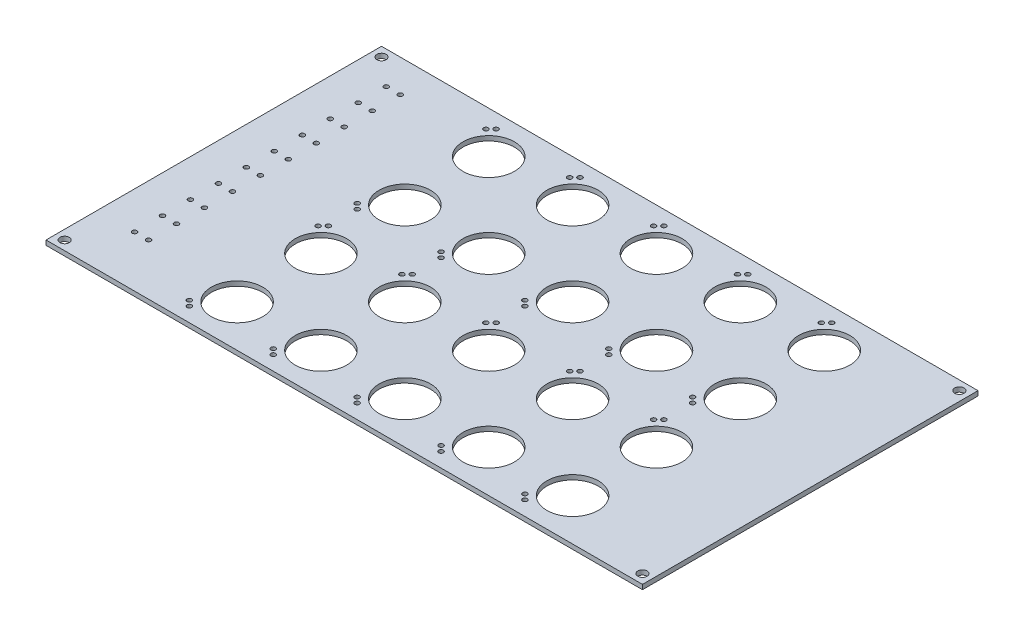
SolidWorks part; units mm, degrees
ref_plane "Front Plane" through (0, 0, 0) normal (0, 0, 1) x (1, 0, 0)
ref_plane "Top Plane" through (0, 0, 0) normal (0, 1, 0) x (1, 0, 0)
ref_plane "Right Plane" through (0, 0, 0) normal (1, 0, 0) x (0, 0, -1)
sketch "Sketch1" plane through (0, 0, 0) normal (0, 1, 0) x (1, 0, 0)
  line L1 (-442.5385, 187.0328) -> (370.2615, 187.0328)
  line L2 (-442.5385, 187.0328) -> (-442.5385, -270.1672)
  line L3 (-442.5385, -270.1672) -> (370.2615, -270.1672)
  line L4 (370.2615, 187.0328) -> (370.2615, -270.1672)
  dimension "D1" = 812.8
  dimension "D2" = 457.2
extrude "Boss-Extrude1" add sketch "Sketch1" along normal blind 6.35
sketch "Sketch3" plane through (0, 6.35, 0) normal (0, 1, 0) x (1, 0, 0)
  line L0 (-442.5385, -270.1672) -> (370.2615, -270.1672) construction
  line L1 (370.2615, -270.1672) -> (370.2615, 187.0328) construction
  line L2 (370.2615, 187.0328) -> (-442.5385, 187.0328) construction
  line L3 (-442.5385, 187.0328) -> (-442.5385, -270.1672) construction
  line L4 (-239.3385, 164.8828) -> (-185.8833, 164.8828) construction
  line L5 (-266.7705, 167.4228) -> (-296.8676, 137.3257) construction
  line L6 (-308.109, 72.7328) -> (304.6709, 72.7328) construction
  line L7 (-266.7705, -21.9572) -> (-296.8676, 8.1399) construction
  line L8 (-442.5385, -41.5672) -> (370.2615, -41.5672) construction
  line L9 (-266.7705, -61.1772) -> (-296.8676, -91.2743) construction
  line L10 (-308.109, -155.8672) -> (304.6709, -155.8672) construction
  line L11 (-266.7705, -250.5572) -> (-296.8676, -220.4601) construction
  line L12 (-239.3385, -248.0172) -> (-185.8833, -248.0172) construction
  circle A0 centre (-239.3385, 129.8828) radius 35
  circle A5 centre (-125.0385, 129.8828) radius 35
  circle A6 centre (-10.7385, 129.8828) radius 35
  circle A7 centre (103.5615, 129.8828) radius 35
  circle A8 centre (217.8615, 129.8828) radius 35
  circle A9 centre (-125.0385, 15.5828) radius 35
  circle A10 centre (-10.7385, 15.5828) radius 35
  circle A11 centre (103.5615, 15.5828) radius 35
  circle A12 centre (217.8615, 15.5828) radius 35
  circle A21 centre (-239.3385, 15.5828) radius 35
  circle A44 centre (-391.7385, 142.5828) radius 3.175
  circle A45 centre (-372.6885, 142.5828) radius 3.175
  circle A46 centre (-372.6885, 104.4828) radius 3.175
  circle A47 centre (-372.6885, 66.3828) radius 3.175
  circle A48 centre (-372.6885, 28.2828) radius 3.175
  circle A49 centre (-372.6885, -9.8172) radius 3.175
  circle A50 centre (-372.6885, -47.9172) radius 3.175
  circle A51 centre (-372.6885, -86.0172) radius 3.175
  circle A52 centre (-372.6885, -124.1172) radius 3.175
  circle A53 centre (-372.6885, -162.2172) radius 3.175
  circle A54 centre (-372.6885, -200.3172) radius 3.175
  circle A55 centre (-391.7385, 104.4828) radius 3.175
  circle A56 centre (-391.7385, 66.3828) radius 3.175
  circle A57 centre (-391.7385, 28.2828) radius 3.175
  circle A58 centre (-391.7385, -9.8172) radius 3.175
  circle A59 centre (-391.7385, -47.9172) radius 3.175
  circle A60 centre (-391.7385, -86.0172) radius 3.175
  circle A61 centre (-391.7385, -124.1172) radius 3.175
  circle A62 centre (-391.7385, -162.2172) radius 3.175
  circle A63 centre (-391.7385, -200.3172) radius 3.175
  circle A64 centre (-429.8385, 174.3328) radius 6.35
  circle A65 centre (-429.8385, -257.4672) radius 6.35
  circle A66 centre (357.5615, -257.4672) radius 6.35
  circle A67 centre (357.5615, 174.3328) radius 6.35
  circle A68 centre (-125.0385, -98.7172) radius 35 [skipped]
  circle A69 centre (-10.7385, -98.7172) radius 35 [skipped]
  circle A70 centre (103.5615, -98.7172) radius 35 [skipped]
  circle A71 centre (217.8615, -98.7172) radius 35 [skipped]
  circle A72 centre (-125.0385, -213.0172) radius 35 [skipped]
  circle A73 centre (-10.7385, -213.0172) radius 35 [skipped]
  circle A74 centre (103.5615, -213.0172) radius 35 [skipped]
  circle A75 centre (-239.3385, -98.7172) radius 35 [skipped]
  circle A76 centre (-239.3385, -213.0172) radius 35 [skipped]
  circle A77 centre (-266.7705, 167.4228) radius 3.175
  circle A79 centre (-273.7751, 160.4182) radius 3.175
  circle A80 centre (-152.4705, 167.4228) radius 3.175
  circle A81 centre (-159.4751, 160.4182) radius 3.175
  circle A82 centre (-38.1705, 167.4228) radius 3.175
  circle A83 centre (-45.1751, 160.4182) radius 3.175
  circle A84 centre (76.1295, 167.4228) radius 3.175
  circle A85 centre (69.1249, 160.4182) radius 3.175
  circle A86 centre (190.4295, 167.4228) radius 3.175
  circle A87 centre (217.8615, -213.0172) radius 35 [skipped]
  circle A88 centre (183.4249, 160.4182) radius 3.175
  circle A89 centre (190.4295, -21.9572) radius 3.175
  circle A90 centre (76.1295, -21.9572) radius 3.175
  circle A91 centre (69.1249, -14.9526) radius 3.175
  circle A92 centre (183.4249, -14.9526) radius 3.175
  circle A93 centre (-38.1705, -21.9572) radius 3.175
  circle A94 centre (-45.1751, -14.9526) radius 3.175
  circle A95 centre (-152.4705, -21.9572) radius 3.175
  circle A96 centre (-159.4751, -14.9526) radius 3.175
  circle A97 centre (-266.7705, -21.9572) radius 3.175
  circle A98 centre (-273.7751, -14.9526) radius 3.175
  circle A99 centre (-273.7751, -68.1818) radius 3.175
  circle A100 centre (-266.7705, -61.1772) radius 3.175
  circle A101 centre (-159.4751, -68.1818) radius 3.175
  circle A102 centre (-152.4705, -61.1772) radius 3.175
  circle A103 centre (-45.1751, -68.1818) radius 3.175
  circle A104 centre (-38.1705, -61.1772) radius 3.175
  circle A105 centre (183.4249, -68.1818) radius 3.175
  circle A106 centre (69.1249, -68.1818) radius 3.175
  circle A107 centre (76.1295, -61.1772) radius 3.175
  circle A108 centre (190.4295, -61.1772) radius 3.175
  circle A109 centre (183.4249, -243.5526) radius 3.175
  circle A110 centre (190.4295, -250.5572) radius 3.175
  circle A111 centre (69.1249, -243.5526) radius 3.175
  circle A112 centre (76.1295, -250.5572) radius 3.175
  circle A113 centre (-45.1751, -243.5526) radius 3.175
  circle A114 centre (-38.1705, -250.5572) radius 3.175
  circle A115 centre (-159.4751, -243.5526) radius 3.175
  circle A116 centre (-152.4705, -250.5572) radius 3.175
  circle A117 centre (-273.7751, -243.5526) radius 3.175
  circle A118 centre (-266.7705, -250.5572) radius 3.175
  circle A119 centre (-239.3385, -98.7172) radius 35
  circle A120 centre (217.8615, -98.7172) radius 35
  circle A121 centre (103.5615, -98.7172) radius 35
  circle A122 centre (-10.7385, -98.7172) radius 35
  circle A123 centre (-125.0385, -98.7172) radius 35
  circle A124 centre (217.8615, -213.0172) radius 35
  circle A125 centre (103.5615, -213.0172) radius 35
  circle A126 centre (-10.7385, -213.0172) radius 35
  circle A127 centre (-125.0385, -213.0172) radius 35
  circle A128 centre (-239.3385, -213.0172) radius 35
  dimension "D3" = 70
  dimension "D14" = 6.35
  dimension "D18" = 12.7
  dimension "D21" = 12.7
  dimension "D23" = 12.7
  dimension "D9" = 6.35
  dimension "D4" = 114.3
  dimension "D5" = 114.3
  dimension "D6" = 57.15
  dimension "D7" = 203.2
  dimension "D10" = 27.432
  dimension "D13" = 19.05
  dimension "D15" = 38.1
  dimension "D16" = 44.45
  dimension "D17" = 50.8
  dimension "D19" = 12.7
  dimension "D20" = 12.7
  dimension "D22" = 12.7
  dimension "D24" = 45
  dimension "D8" = 2.54
  dimension "D25" = 9.906
  dimension "D27" = 57.15
  dimension "D1" = 5
  dimension "D2" = 4
  dimension "D11" = 2
  dimension "D12" = 10
  dimension "D26" = 5
extrude "Cut-Extrude1" cut sketch "Sketch3" against normal blind 6.35
sketch "Sketch4" plane through (0, 6.35, 0) normal (0, 1, 0) x (1, 0, 0)
  line L0 (-280.5081, 153.6852) -> (-256.9683, 177.225) construction
  line L1 (-282.6472, 162.1527) -> (-268.5051, 176.2948)
  line L2 (-282.6472, 162.1527) -> (-272.0406, 151.5461)
  line L3 (-268.5051, 176.2948) -> (-257.8985, 165.6882)
  line L4 (-272.0406, 151.5461) -> (-257.8985, 165.6882)
  line L5 (-263.2018, 170.9915) -> (-277.3439, 156.8494) construction
  line L6 (-275.5761, 169.2238) -> (-264.9695, 158.6172) construction
  line L7 (-157.7406, 151.5461) -> (-143.5985, 165.6882)
  line L8 (-168.3472, 162.1527) -> (-157.7406, 151.5461)
  line L9 (-168.3472, 162.1527) -> (-154.2051, 176.2948)
  line L10 (-154.2051, 176.2948) -> (-143.5985, 165.6882)
  line L11 (-43.4406, 151.5461) -> (-29.2985, 165.6882)
  line L12 (-54.0472, 162.1527) -> (-43.4406, 151.5461)
  line L13 (-54.0472, 162.1527) -> (-39.9051, 176.2948)
  line L14 (-39.9051, 176.2948) -> (-29.2985, 165.6882)
  line L15 (70.8594, 151.5461) -> (85.0015, 165.6882)
  line L16 (60.2528, 162.1527) -> (70.8594, 151.5461)
  line L17 (60.2528, 162.1527) -> (74.3949, 176.2948)
  line L18 (74.3949, 176.2948) -> (85.0015, 165.6882)
  line L19 (185.1594, 151.5461) -> (199.3015, 165.6882)
  line L20 (174.5528, 162.1527) -> (185.1594, 151.5461)
  line L21 (174.5528, 162.1527) -> (188.6949, 176.2948)
  line L22 (188.6949, 176.2948) -> (199.3015, 165.6882)
  line L23 (-323.3738, 72.7328) -> (296.0257, 72.7328) construction
  line L24 (188.6949, -30.8293) -> (199.3015, -20.2227)
  line L25 (174.5528, -16.6872) -> (188.6949, -30.8293)
  line L26 (174.5528, -16.6872) -> (185.1594, -6.0806)
  line L27 (185.1594, -6.0806) -> (199.3015, -20.2227)
  line L28 (74.3949, -30.8293) -> (85.0015, -20.2227)
  line L29 (60.2528, -16.6872) -> (74.3949, -30.8293)
  line L30 (60.2528, -16.6872) -> (70.8594, -6.0806)
  line L31 (70.8594, -6.0806) -> (85.0015, -20.2227)
  line L32 (-39.9051, -30.8293) -> (-29.2985, -20.2227)
  line L33 (-54.0472, -16.6872) -> (-39.9051, -30.8293)
  line L34 (-54.0472, -16.6872) -> (-43.4406, -6.0806)
  line L35 (-43.4406, -6.0806) -> (-29.2985, -20.2227)
  line L36 (-154.2051, -30.8293) -> (-143.5985, -20.2227)
  line L37 (-157.7406, -6.0806) -> (-143.5985, -20.2227)
  line L38 (-168.3472, -16.6872) -> (-154.2051, -30.8293)
  line L39 (-168.3472, -16.6872) -> (-157.7406, -6.0806)
  line L40 (-272.0406, -6.0806) -> (-257.8985, -20.2227)
  line L41 (-268.5051, -30.8293) -> (-257.8985, -20.2227)
  line L42 (-282.6472, -16.6872) -> (-268.5051, -30.8293)
  line L43 (-282.6472, -16.6872) -> (-272.0406, -6.0806)
  line L44 (-442.5385, -41.5672) -> (370.2615, -41.5672) construction
  line L45 (-442.5385, 187.0328) -> (-442.5385, -270.1672) construction
  line L46 (370.2615, -270.1672) -> (370.2615, 187.0328) construction
  circle A0 centre (-125.0385, 129.8828) radius 35 construction
  point P2 (-266.7705, 167.4228)
  point P4 (-273.7751, 160.4182)
  point P12 (-270.2728, 163.9205)
  dimension "D5" = 57.15
  dimension "D1" = 20
  dimension "D2" = 15
  dimension "D3" = 4.953
  dimension "D4" = 5
